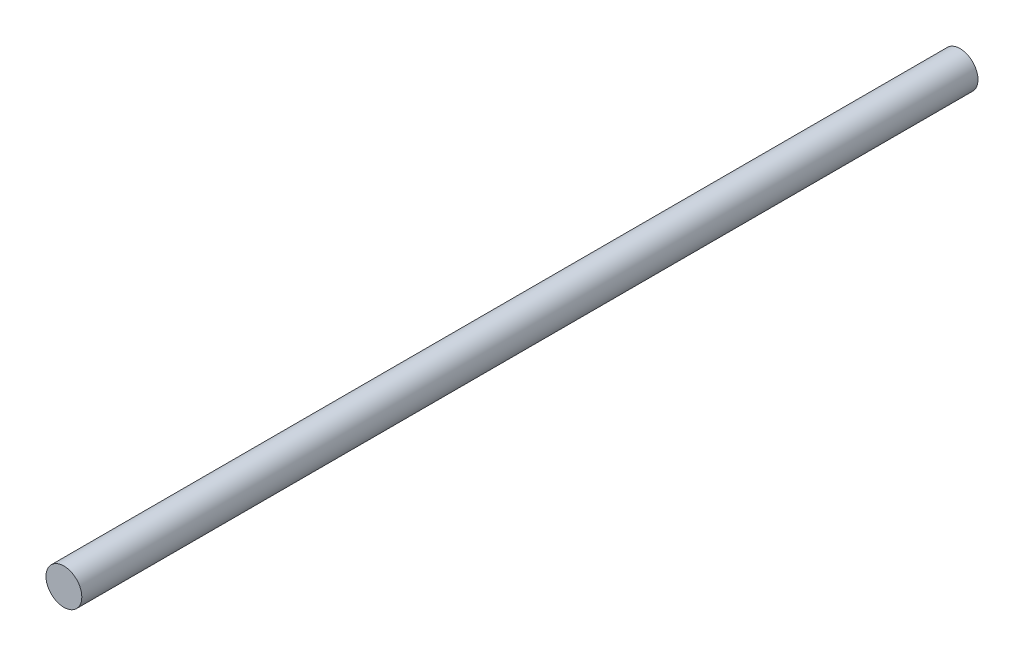
SolidWorks part; units mm, degrees
ref_plane "Спереди" through (0, 0, 0) normal (0, 0, 1) x (1, 0, 0)
ref_plane "Сверху" through (0, 0, 0) normal (0, 1, 0) x (1, 0, 0)
ref_plane "Справа" through (0, 0, 0) normal (1, 0, 0) x (0, 0, -1)
sketch "Sketch1" plane through (0, 0, 0) normal (0, 0, 1) x (1, 0, 0)
  circle A0 centre (0, 0) radius 10
  dimension "D1" = 20
extrude "Boss-Extrude1" add sketch "Sketch1" along normal blind 500
